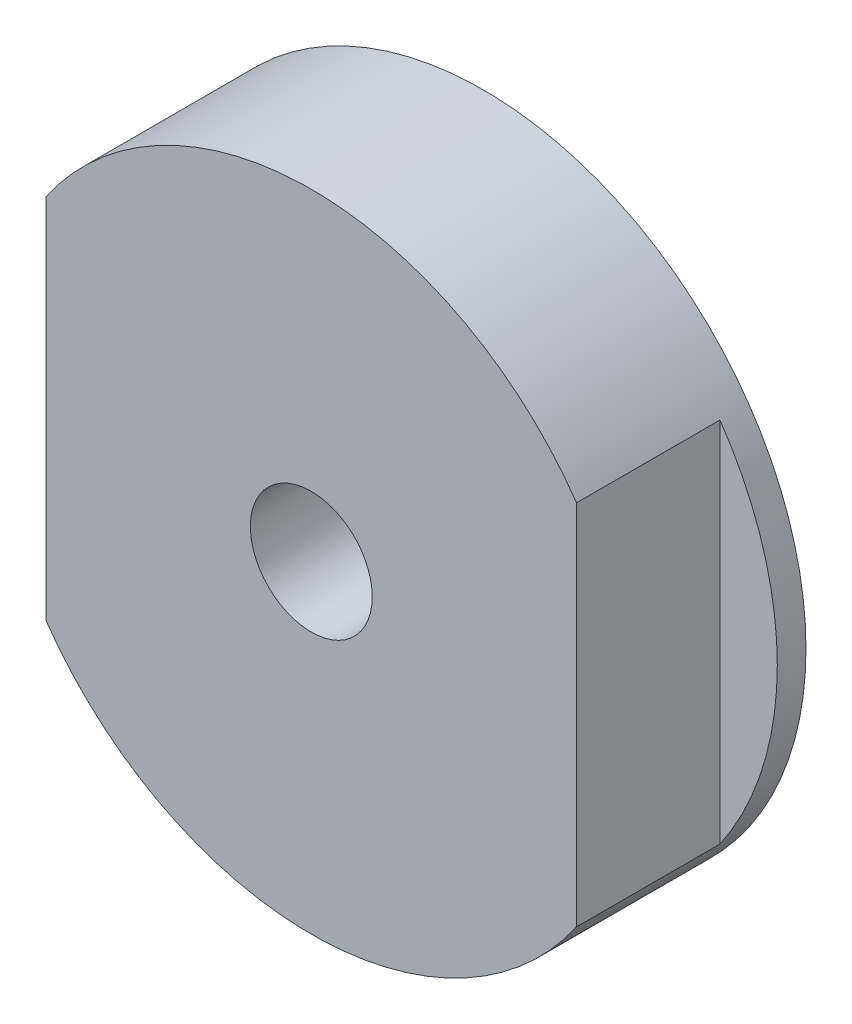
SolidWorks part; units mm, degrees
material "6061 合金"
ref_plane "前视基准面" through (0, 0, 0) normal (0, 0, 1) x (1, 0, 0)
ref_plane "上视基准面" through (0, 0, 0) normal (0, 1, 0) x (1, 0, 0)
ref_plane "右视基准面" through (0, 0, 0) normal (1, 0, 0) x (0, 0, -1)
other "Configuration Table"
sketch "草图1" plane through (0, 0, 0) normal (0, 0, 1) x (1, 0, 0)
  circle A0 centre (0, 0) radius 22.5
  dimension "D1" = 45
extrude "凸台-拉伸1" add sketch "草图1" along normal blind 12
sketch "草图2" plane through (0, 0, 12) normal (0, 0, 1) x (1, 0, 0)
  line L0 (-18.5, 12.8062) -> (-18.5, -12.8062)
  line L1 (0, 0) -> (0, -22.5) construction
  line L2 (18.5, 12.8062) -> (18.5, -12.8062)
  circle A0 centre (0, 0) radius 22.5 construction
  arc A1 (-18.5, 12.8062) -> (-18.5, -12.8062) centre (0, 0) ccw
  arc A2 (18.5, -12.8062) -> (18.5, 12.8062) centre (0, 0) ccw
  dimension "D1" = 37
extrude "切除-拉伸1" cut sketch "草图2" against normal blind 10
sketch "草图3" plane through (0, 0, 12) normal (0, 0, 1) x (1, 0, 0)
  circle A0 centre (0, 0) radius 5
  dimension "D1" = 10
hole_wizard "M10 螺纹孔1" positions "3D草图1" profile "草图4" tap size "M10" standard "GB"
sketch3d "3D草图1"
  point P0 (0, 0, 12)
sketch "草图4" plane through (0, 0, 12) normal (1, 0, 0) x (0, -1, 0)
  line L0 (0, 0) -> (0, 27.0537)
  line L1 (0, 27.0537) -> (4.25, 24.5)
  line L2 (4.25, 24.5) -> (4.25, 0)
  line L5 (4.25, 0) -> (0, 0)
  line L10 (0, 27.0537) -> (-4.25, 24.5) construction
  line L11 (0, -6.35) -> (0, 107.95) construction
  dimension "螺纹孔钻头直径" = 8.5
  dimension "螺纹孔钻头深度" = 24.5
  dimension "导头角度" = 118
cosmetic thread "孔螺蚊线1" parameters "D1"=20, "D2"=10
sketch "草图5" plane through (0, 0, 0) normal (0, 0, -1) x (-1, 0, 0)
  line L0 (12.0208, 12.0208) -> (0, 0) construction
  line L1 (0, 0) -> (17, 0) construction
  circle A0 centre (0, 0) radius 17 construction
  circle A1 centre (12.0208, 12.0208) radius 2
  point P3 (12.0208, 12.0208)
  dimension "D1" = 34
  dimension "D3" = 4
  dimension "D2" = 45
hole_wizard "M4 螺纹孔2" positions "3D草图2" profile "草图7" tap size "M4" standard "GB"
sketch3d "3D草图2"
  point P0 (-12.0208, 12.0208, 0)
cosmetic thread "孔螺蚊线2" parameters "D2"=4
sketch "草图7" plane through (-12.0208, 12.0208, 0) normal (1, 0, 0) x (0, 1, 0)
  line L0 (0, 0) -> (0, 11.0914)
  line L1 (0, 11.0914) -> (1.65, 10.1)
  line L2 (1.65, 10.1) -> (1.65, 0)
  line L5 (1.65, 0) -> (0, 0)
  line L10 (0, 11.0914) -> (-1.65, 10.1) construction
  line L11 (0, -6.35) -> (0, 107.95) construction
  dimension "螺纹孔钻头直径" = 3.3
  dimension "螺纹孔钻头深度" = 10.1
  dimension "导头角度" = 118
pattern_circular "阵列(圆周)1" count 4 over 360 about axis through (0, 0, 0) along (0, 0, 1) of "M4 螺纹孔2"
